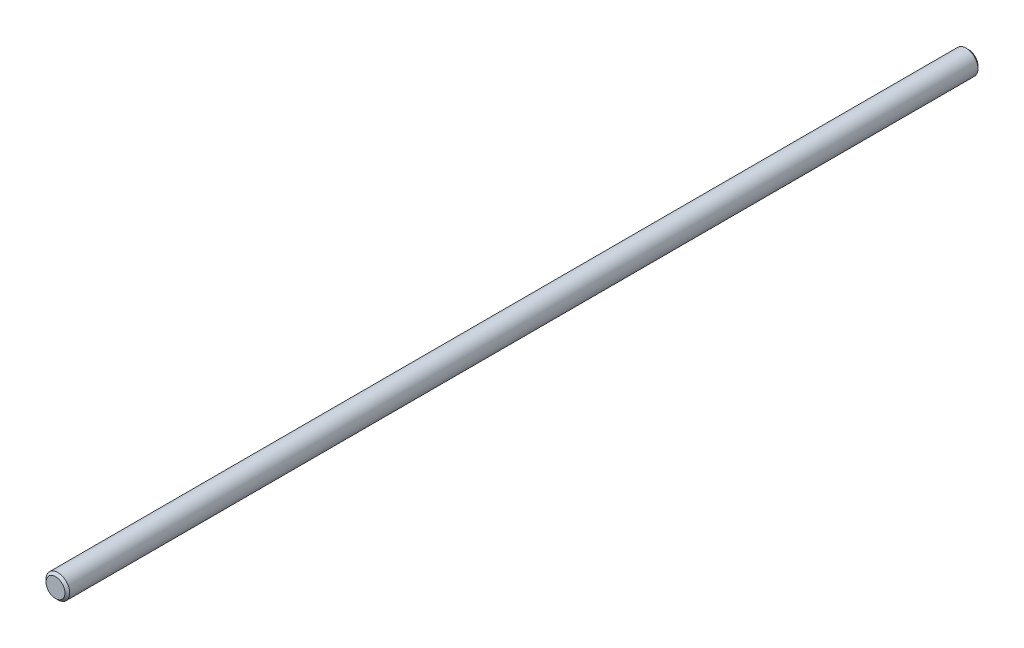
SolidWorks part; units mm, degrees
ref_plane "Plan de face" through (0, 0, 0) normal (0, 0, 1) x (1, 0, 0)
ref_plane "Plan de dessus" through (0, 0, 0) normal (0, 1, 0) x (1, 0, 0)
ref_plane "Plan de droite" through (0, 0, 0) normal (1, 0, 0) x (0, 0, -1)
sketch "Sketch1" plane through (0, 0, 0) normal (0, 0, 1) x (1, 0, 0)
  circle A0 centre (0, 0) radius 3.175
  dimension "D1" = 6.35
extrude "Boss-Extrude1" add sketch "Sketch1" along normal mid plane 244.475
chamfer "Chamfer1" distance 0.635 angle 45 2 edges at (3.175, 0, -122.2375) (3.175, 0, 122.2375)
equation "\"Cout/Uni\"= ( ( \"Coût Achat\" + \"Coût Modif\" ) / \"Nb/Paquet\" )"
